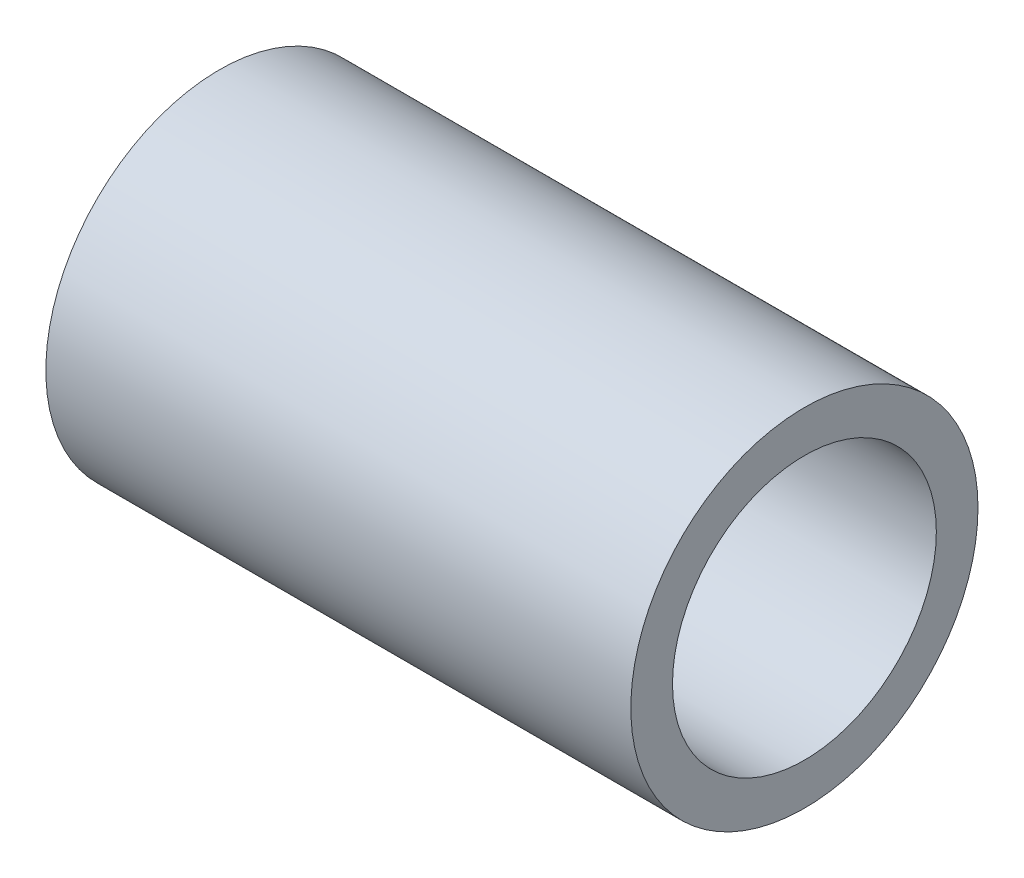
SolidWorks part; units mm, degrees
ref_plane "Front Plane" through (0, 0, 0) normal (0, 0, 1) x (1, 0, 0)
ref_plane "Top Plane" through (0, 0, 0) normal (0, 1, 0) x (1, 0, 0)
ref_plane "Right Plane" through (0, 0, 0) normal (1, 0, 0) x (0, 0, -1)
sketch "Sketch1" plane through (0, 0, 0) normal (1, 0, 0) x (0, 0, -1)
  circle A0 centre (0, 0) radius 6.35
  circle A1 centre (0, 0) radius 4.826
  dimension "D1" = 12.7
  dimension "D2" = 9.652
extrude "Boss-Extrude1" add sketch "Sketch1" along normal blind 21.3995
